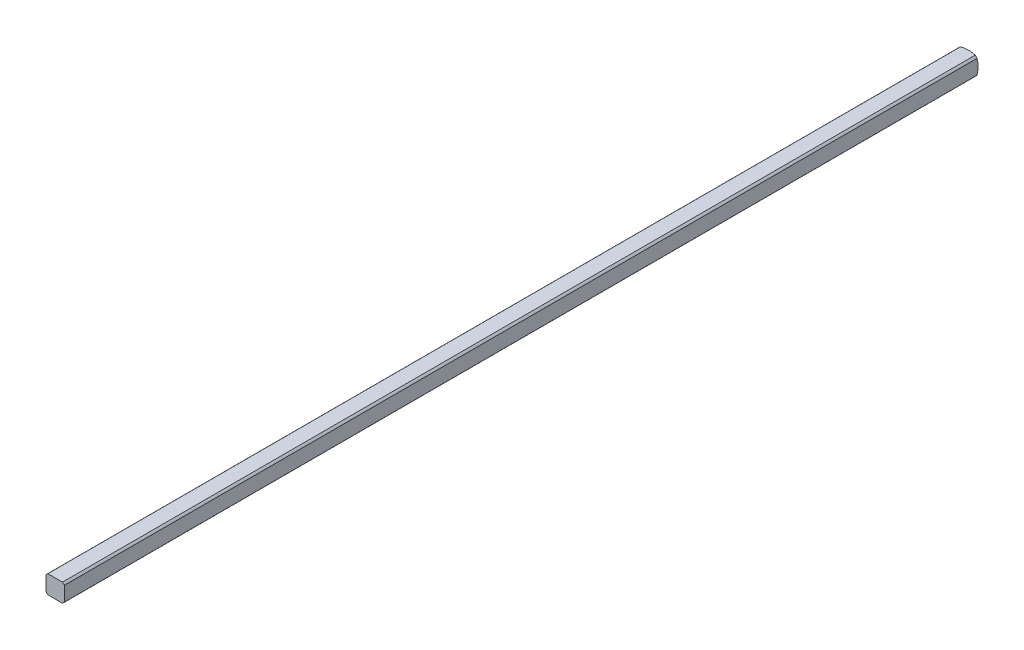
SolidWorks part; units mm, degrees
material "Custom Plastic"
ref_plane "Front Plane" through (0, 0, 0) normal (0, 0, 1) x (1, 0, 0)
ref_plane "Top Plane" through (0, 0, 0) normal (0, 1, 0) x (1, 0, 0)
ref_plane "Right Plane" through (0, 0, 0) normal (1, 0, 0) x (0, 0, -1)
sketch "Sketch1" plane through (0, 0, 0) normal (0, 0, 1) x (1, 0, 0)
  line L0 (-1.5875, -1.5875) -> (1.5875, 1.5875) construction
  line L1 (-1.5875, -1.5875) -> (1.5875, -1.5875)
  line L2 (-1.5875, -1.5875) -> (-1.5875, 1.5875)
  line L3 (-1.5875, 1.5875) -> (1.5875, 1.5875)
  line L4 (1.5875, -1.5875) -> (1.5875, 1.5875)
  dimension "D1" = 3.175
extrude "Boss-Extrude1" add sketch "Sketch1" along normal blind 152.4
sketch "Sketch2" plane through (0, 0, 0) normal (0, 0, -1) x (-1, 0, 0)
  circle A0 centre (0, 0) radius 2.032
  dimension "D1" = 4.064
extrude "Cut-Extrude1" cut sketch "Sketch2" against normal through all flip side to cut
ref_axis "Axis1" through (0, 0, 152.4) along (0, 0, -1)
sketch "Sketch3" plane through (0, 0, 0) normal (0, 1, 0) x (1, 0, 0)
  line L1 (-5.0537, -4.4027) -> (-5.0537, 5.7405)
  line L2 (-5.0537, 5.7405) -> (0, 5.7405)
  line L5 (0, -152.4) -> (0, 0) construction
  line L8 (0, 0.1609) -> (0, 5.7405)
  arc A0 (-5.0537, -4.4027) -> (0, 0.1609) centre (0, -4.9191) cw
  dimension "D1" = 5.08
revolve "Cut-Revolve1" cut sketch "Sketch3" angle 360 about axis through (0, 0, 152.4) along (0, 0, -1)
mirror "Mirror1" about plane through (0, 0, 152.4) normal (0, 0, -1) of bodies 103
sketch "Sketch4" plane through (1.5875, 0, 0) normal (1, 0, 0) x (0, 0, -1)
  line L0 (-304.5368, -1.5875) -> (-158.4868, -1.5875)
  line L1 (-304.5368, -1.5875) -> (-0.2632, -1.5875) construction
  line L2 (-158.4868, -1.5875) -> (-158.4868, 1.5875)
  line L3 (-0.2632, 1.5875) -> (-304.5368, 1.5875) construction
  line L4 (-158.4868, 1.5875) -> (-304.7065, 1.5875)
  line L5 (-304.5368, 1.5875) -> (-304.7065, 1.5875) construction
  line L6 (-304.7065, 1.5875) -> (-304.8, 1.2683)
  line L7 (-304.8, 1.2683) -> (-304.8, -1.2683)
  line L8 (-304.8, 1.2683) -> (-304.8, -1.2683) construction
  line L9 (-304.8, -1.2683) -> (-304.5368, -1.5875)
  arc A0 (-304.7065, 1.5875) -> (-304.8, 1.2683) centre (-299.8809, 0) ccw construction
  dimension "D1" = 146.05
extrude "Cut-Extrude3" cut sketch "Sketch4" against normal through all
